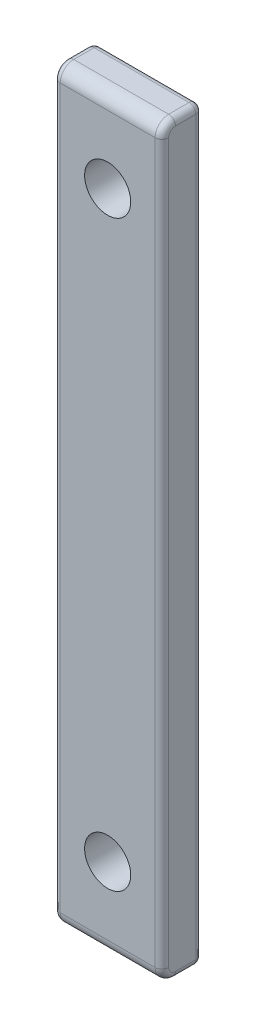
SolidWorks part; units mm, degrees
ref_plane "Front Plane" through (0, 0, 0) normal (1, 0, 0) x (0, 1, 0)
ref_plane "Top Plane" through (0, 0, 0) normal (0, 0, 1) x (0, 1, 0)
ref_plane "Right Plane" through (0, 0, 0) normal (0, 1, 0) x (-1, 0, 0)
sketch "Sketch1" plane through (0, 0, 0) normal (0, 0, 1) x (0, 1, 0)
  line L1 (27.5, 4) -> (-27.5, 4)
  line L2 (27.5, 4) -> (27.5, -4)
  line L3 (27.5, -4) -> (-27.5, -4)
  line L4 (-27.5, 4) -> (-27.5, -4)
  line L5 (27.5, 4) -> (-27.5, -4) construction
  line L6 (27.5, -4) -> (-27.5, 4) construction
  point P0 (0, 0)
  dimension "D1" = 8
  dimension "D2" = 55
extrude "Boss-Extrude1" add sketch "Sketch1" along normal blind 3
ref_plane "Plane1" through (0, 0, 3) normal (0, 0, 1) x (1, 0, 0)
sketch "Sketch2" plane through (0, 0, 3) normal (0, 0, 1) x (1, 0, 0)
  line L1 (-4, 27.5) -> (-4, -27.5) construction
  line L2 (4, 0) -> (-4, 0) construction
  line L3 (4, 27.5) -> (-4, 27.5) construction
  circle A0 centre (0, 21.5) radius 1.7
  circle A1 centre (0, -21.5) radius 1.7
  point P10 (0, 0)
  dimension "D1" = 3.4
  dimension "D2" = 6
  dimension "D3" = 4
extrude "Cut-Extrude1" cut sketch "Sketch2" against normal blind 3
fillet "Fillet2" radius 1 2 edges at (0, -27.5, 3) (0, 27.5, 3)
fillet "Fillet3" radius 0.5 10 edges at (4, -27.5, 1) (4, -27.2071, 2.7071) (4, 27.5, 1) (4, 27.2071, 2.7071) (-4, 27.5, 1) (-4, 27.2071, 2.7071) (-4, -27.5, 1) (-4, -27.2071, 2.7071) (4, 0, 3) (-4, 0, 3)
fillet "Fillet4" radius 0.5 8 edges at (3.8536, 27.3536, 0) (4, 0, 0) (3.8536, -27.3536, 0) (0, -27.5, 0) (-3.8536, -27.3536, 0) (-4, 0, 0) (-3.8536, 27.3536, 0) (0, 27.5, 0)
